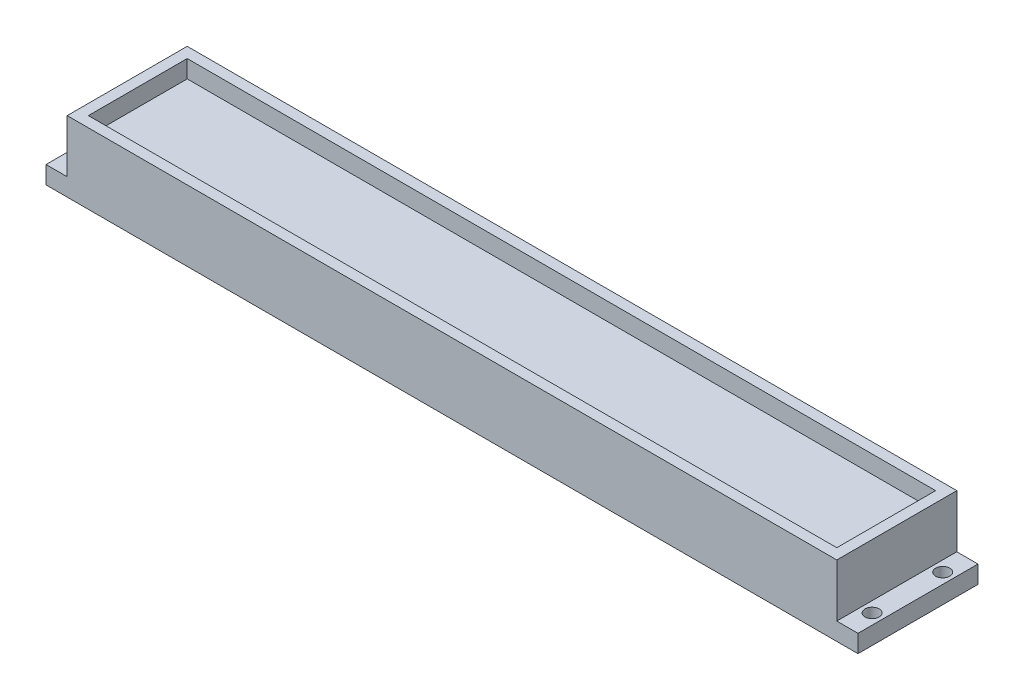
SolidWorks part; units mm, degrees
ref_plane "Front Plane" through (0, 0, 0) normal (0, 0, 1) x (1, 0, 0)
ref_plane "Top Plane" through (0, 0, 0) normal (0, 1, 0) x (1, 0, 0)
ref_plane "Right Plane" through (0, 0, 0) normal (1, 0, 0) x (0, 0, -1)
sketch "Sketch1" plane through (0, 0, 0) normal (0, 0, 1) x (1, 0, 0)
  line L0 (0, 0) -> (230, 0)
  line L1 (230, 0) -> (230, 5)
  line L2 (230, 5) -> (224, 5)
  line L3 (0, 0) -> (0, 5)
  line L4 (0, 5) -> (6, 5)
  line L5 (6, 5) -> (6, 20)
  line L6 (6, 20) -> (9, 20)
  line L7 (224, 20) -> (224, 5)
  line L8 (9, 20) -> (9, 15)
  line L9 (224, 20) -> (221, 20)
  line L10 (221, 20) -> (221, 15)
  line L11 (221, 15) -> (9, 15)
extrude "Boss-Extrude1" add sketch "Sketch1" along normal blind 34
sketch "Sketch2" plane through (0, 20, 0) normal (0, 1, 0) x (1, 0, 0)
  line L0 (9, 0) -> (221, 0)
  line L1 (221, 0) -> (221, -3)
  line L2 (221, -34) -> (221, 0) construction
  line L3 (221, -3) -> (9, -3)
  line L4 (9, -34) -> (9, 0) construction
  line L5 (9, -3) -> (9, 0)
  line L6 (9, -34) -> (9, -31)
  line L7 (9, -34) -> (9, 0) construction
  line L8 (9, -31) -> (221, -31)
  line L9 (221, -31) -> (221, -34)
  line L10 (221, -34) -> (9, -34)
extrude "Boss-Extrude2" add sketch "Sketch2" against normal up to next
sketch "Sketch3" plane through (0, 5, 0) normal (0, 1, 0) x (1, 0, 0)
  line L0 (6, 0) -> (0, 0) construction
  line L2 (0, -34) -> (0, 0) construction
  line L3 (115, 0) -> (115, -37.6792) construction
  line L4 (224, 0) -> (6, 0) construction
  circle A0 centre (3, -7) radius 2
  circle A1 centre (3, -27) radius 2
  circle A2 centre (227, -27) radius 2
  circle A3 centre (227, -7) radius 2
  dimension "D1" = 20
  dimension "D2" = 7
  dimension "D3" = 3
extrude "Cut-Extrude1" cut sketch "Sketch3" against normal up to next
